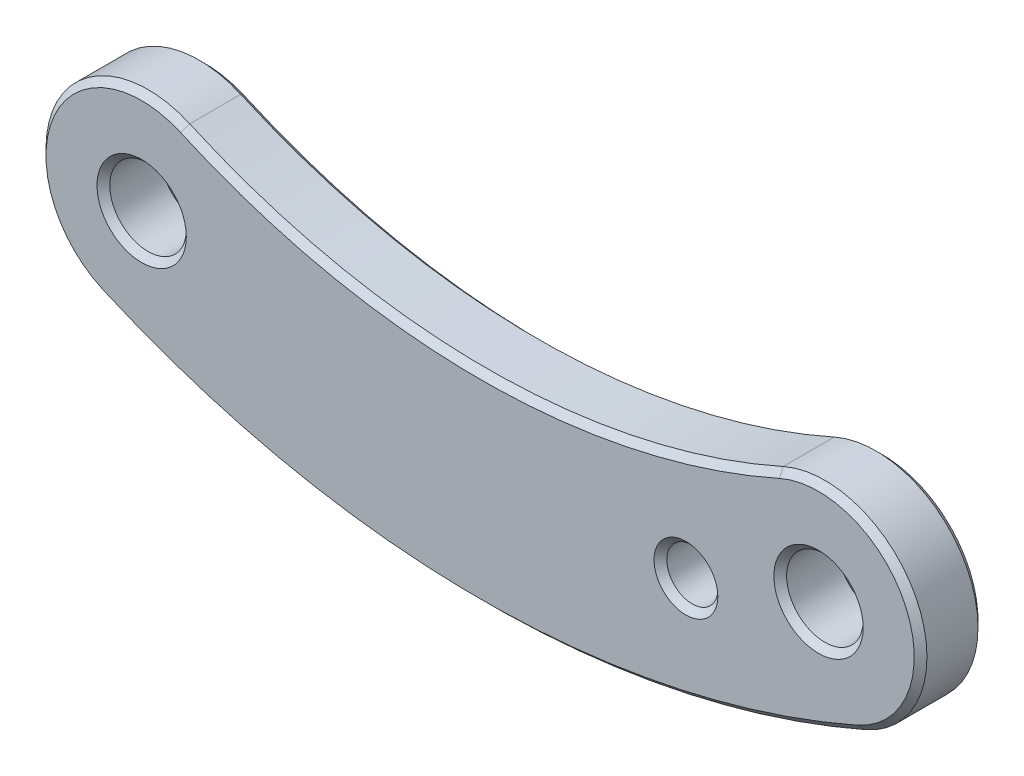
SolidWorks part; units mm, degrees
ref_plane "前视基准面" through (0, 0, 0) normal (0, 0, 1) x (1, 0, 0)
ref_plane "上视基准面" through (0, 0, 0) normal (0, 1, 0) x (1, 0, 0)
ref_plane "右视基准面" through (0, 0, 0) normal (1, 0, 0) x (0, 0, -1)
sketch "草图1" plane through (0, 0, 0) normal (0, 0, 1) x (1, 0, 0)
  line L0 (-53.06, 0) -> (0, 0) construction
  circle A0 centre (0, 0) radius 3
  circle A1 centre (-53.06, 0) radius 3
  arc A2 (-56.2758, -7.3252) -> (-49.7948, 7.3033) centre (-53.06, 0) cw
  arc A3 (3.2158, -7.3252) -> (-3.2652, 7.3033) centre (0, 0) ccw
  arc A4 (-56.2758, -7.3252) -> (3.2158, -7.3252) centre (-26.53, 60.4331) ccw
  arc A5 (-49.7948, 7.3033) -> (-3.2652, 7.3033) centre (-26.53, 59.3394) ccw
  dimension "D1" = 6
  dimension "D2" = 8
  dimension "D4" = 74
  dimension "D5" = 57
  dimension "D3" = 53.06
extrude "凸台-拉伸1" add sketch "草图1" along normal blind 5
chamfer "倒角1" distance 0.5 angle 45 12 edges at (3, 0, 5) (3, 0, 0) (-50.06, 0, 0) (-50.06, 0, 5) (-26.53, 2.3394, 0) (-60.3743, 3.2405, 0) (7.3143, 3.2405, 0) (-26.53, -13.5669, 0) (-26.53, 2.3394, 5) (-60.3743, 3.2405, 5) (7.3143, 3.2405, 5) (-26.53, -13.5669, 5)
sketch "草图2" plane through (0, 0, 0) normal (0, 0, -1) x (-1, 0, 0)
  line L0 (0, 0) -> (10.396, -3.5949) construction
  line L1 (13.0104, 3.9659) -> (7.7826, -11.1527) construction
  circle A0 centre (10.396, -3.5949) radius 2
  arc A3 (3.2652, 7.3033) -> (49.7948, 7.3033) centre (26.53, 59.3394) ccw construction
  arc A4 (-3.2158, -7.3252) -> (56.2758, -7.3252) centre (26.53, 60.4331) ccw construction
  point P12 (26.53, -5.0798)
  point P13 (11.3951, -4.2507)
  point P14 (8.8944, -13.5669)
  point P15 (10.723, -3.4107)
  point P16 (14.2363, -2.8158)
  dimension "D1" = 4
  dimension "D2" = 11
  dimension "D3" = 8
extrude "切除-拉伸1" cut sketch "草图2" against normal through all both and the other way through all
chamfer "倒角2" distance 0.5 angle 45 2 edges at (-8.396, -3.5949, 0) (-12.396, -3.5949, 5)
